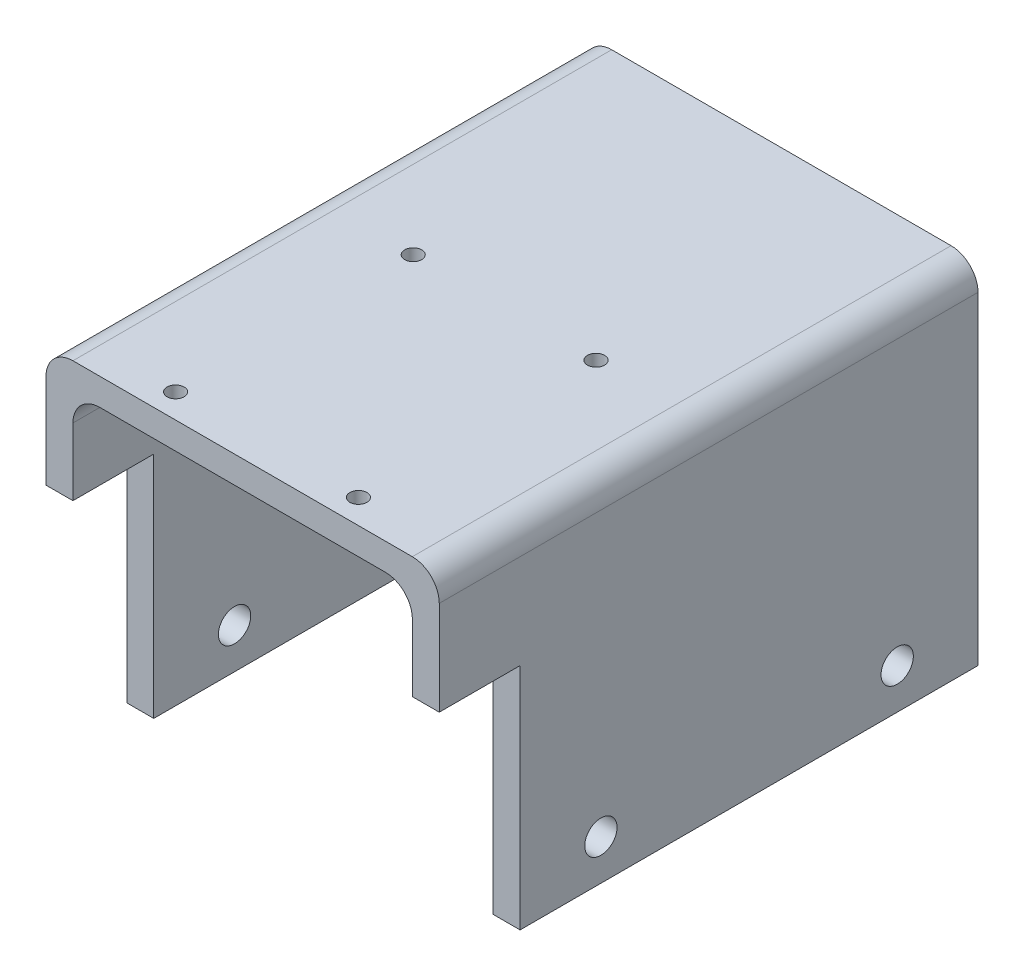
SolidWorks part; units mm, degrees
ref_plane "Alzado" through (0, 0, 0) normal (0, 0, 1) x (1, 0, 0)
ref_plane "Planta" through (0, 0, 0) normal (0, 1, 0) x (1, 0, 0)
ref_plane "Vista lateral" through (0, 0, 0) normal (1, 0, 0) x (0, 0, -1)
sketch "Croquis1" plane through (0, 0, 0) normal (0, 0, 1) x (1, 0, 0)
  line L0 (-136, 0) -> (-126, 0)
  line L1 (-126, 0) -> (-126, 120)
  line L2 (-126, 120) -> (0, 120)
  line L3 (0, 120) -> (0, 0)
  line L4 (0, 0) -> (10, 0)
  line L5 (10, 0) -> (10, 130)
  line L6 (10, 130) -> (-136, 130)
  line L7 (-136, 130) -> (-136, 0)
  dimension "D1" = 126
  dimension "D2" = 10
  dimension "D3" = 10
  dimension "D4" = 10
  dimension "D5" = 0
  dimension "D6" = 0
  dimension "D7" = 130
extrude "Saliente-Extruir1" add sketch "Croquis1" along normal blind 200
fillet "Redondeo1" radius 10 4 edges at (0, 120, 100) (-126, 120, 100) (10, 130, 100) (-136, 130, 100)
sketch "Croquis2" plane through (10, 0, 0) normal (1, 0, 0) x (0, 0, -1)
  line L0 (-200, 0) -> (-200, 120) construction
  line L1 (0, 0) -> (0, 120) construction
  line L2 (-200, 0) -> (0, 0) construction
  circle A0 centre (-140, 15) radius 6
  circle A1 centre (-30, 15) radius 6
  dimension "D1" = 12
  dimension "D2" = 12
  dimension "D3" = 60
  dimension "D4" = 30
  dimension "D5" = 15
  dimension "D6" = 15
extrude "Cortar-Extruir1" cut sketch "Croquis2" against normal through all
sketch "Croquis3" plane through (10, 0, 0) normal (1, 0, 0) x (0, 0, -1)
  line L0 (-200, 85) -> (-170, 85)
  line L1 (-200, 0) -> (-200, 120) construction
  line L2 (-170, 85) -> (-170, 0)
  line L3 (-200, 0) -> (0, 0) construction
  line L4 (-170, 0) -> (-200, 0)
  line L5 (-200, 0) -> (-200, 85)
  dimension "D1" = 30
  dimension "D2" = 85
extrude "Cortar-Extruir2" cut sketch "Croquis3" against normal through all
sketch "Croquis4" plane through (0, 130, 0) normal (0, 1, 0) x (1, 0, 0)
  line L0 (-126, 0) -> (-126, -200) construction
  line L1 (0, -200) -> (-126, -200) construction
  circle A0 centre (-96.928, -190.953) radius 3.1665
  circle A1 centre (-29.072, -190.953) radius 3.1665
  circle A2 centre (-96.928, -102.741) radius 3.1665
  circle A3 centre (-29.072, -102.741) radius 3.1665
  point P8 (0, 0)
  point P9 (0, 0)
  point P10 (0, 0)
  point P11 (0, 0)
  point P12 (-99.8415, -171.2516)
  point P15 (-104.7839, -168.0391)
  dimension "D6" = 6.333
  dimension "D7" = 6.333
  dimension "D8" = 6.333
  dimension "D9" = 6.333
  dimension "D1" = 67.856
  dimension "D2" = 67.856
  dimension "D3" = 88.212
  dimension "D4" = 29.072
  dimension "D5" = 9.047
extrude "Cortar-Extruir3" cut sketch "Croquis4" against normal up to next
